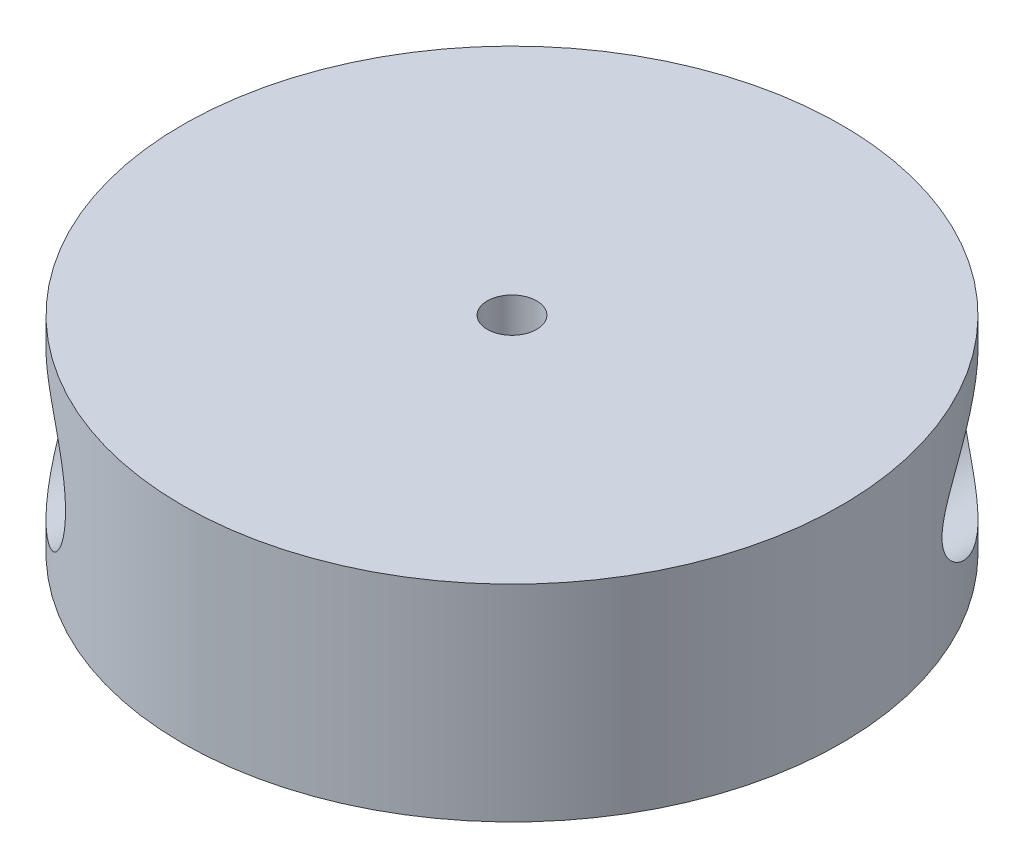
SolidWorks part; units mm, degrees
ref_plane "Front Plane" through (0, 0, 0) normal (0, 0, 1) x (1, 0, 0)
ref_plane "Top Plane" through (0, 0, 0) normal (0, 1, 0) x (1, 0, 0)
ref_plane "Right Plane" through (0, 0, 0) normal (1, 0, 0) x (0, 0, -1)
sketch "Sketch1" plane through (0, 0, 0) normal (0, 1, 0) x (1, 0, 0)
  circle A0 centre (0, 0) radius 40
  circle A1 centre (0, 0) radius 3
  dimension "D1" = 80
  dimension "D2" = 6
extrude "Boss-Extrude1" add sketch "Sketch1" along normal blind 25
sketch "Sketch2" plane through (0, 0, 0) normal (0, -1, 0) x (1, 0, 0)
  circle A0 centre (0, 0) radius 7
  circle A1 centre (0, 0) radius 3
  dimension "D1" = 14
  dimension "D2" = 6
extrude "Boss-Extrude2" add sketch "Sketch2" along normal blind 15
sketch "Sketch3" plane through (0, 0, 0) normal (0, 0, 1) x (1, 0, 0)
  line L0 (0, 25) -> (0, 0) construction
  line L1 (3, 25) -> (-3, 25) construction
  line L2 (-40, 12.5) -> (40, 12.5) construction
  line L3 (-40, 25) -> (-40, 0) construction
  line L4 (40, 0) -> (40, 25) construction
  line L5 (-40, 12.5) -> (0, 12.5) construction
  line L6 (0, 12.5) -> (40, 12.5) construction
  circle A0 centre (28, 12.5) radius 9
  dimension "D1" = 18
  dimension "D2" = 12
extrude "Cut-Extrude1" cut sketch "Sketch3" against normal through all
sketch "Sketch4" plane through (0, 0, 0) normal (0, 0, 1) x (1, 0, 0)
  line L0 (40, 25) -> (-40, 25) construction
  line L1 (-40, 25) -> (-40, 0) construction
  circle A0 centre (-28, 12.5) radius 9
  dimension "D1" = 18
  dimension "D2" = 12.5
  dimension "D3" = 12
extrude "Cut-Extrude2" cut sketch "Sketch4" along normal through all
